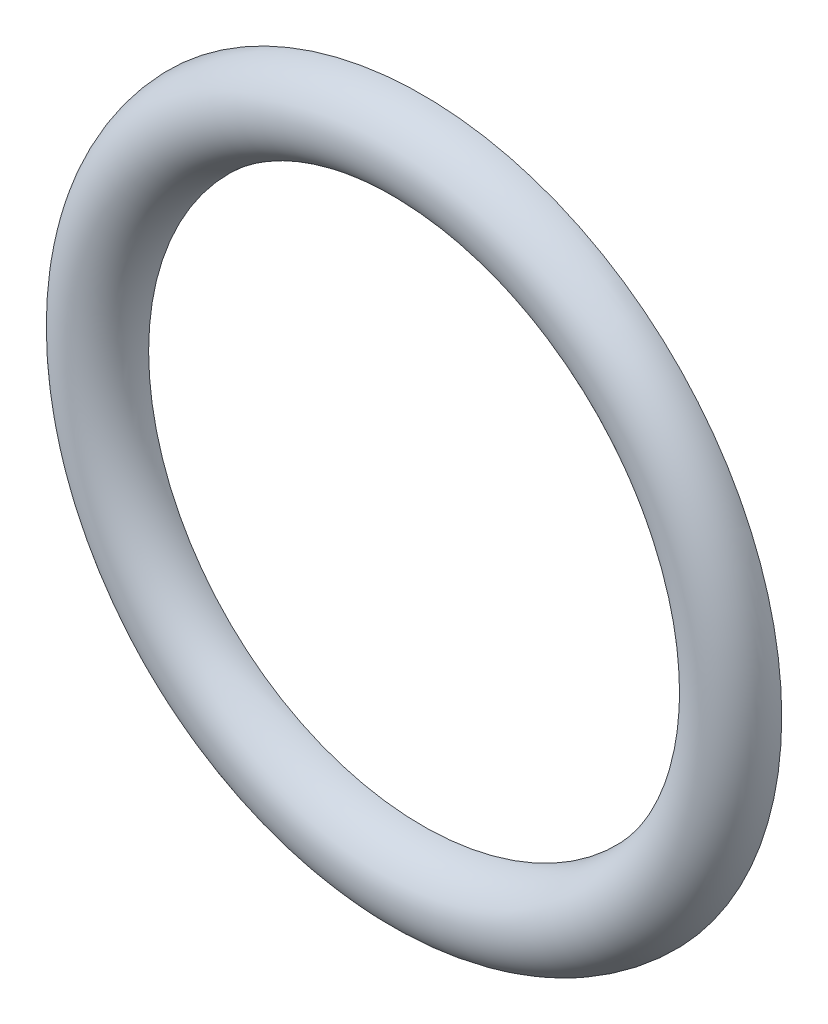
SolidWorks part; units mm, degrees
material "Delrin 2700 NC010, Low Viscosity Acetal Copolymer (SS)"
ref_plane "Front Plane" through (0, 0, 0) normal (0, 0, 1) x (1, 0, 0)
ref_plane "Top Plane" through (0, 0, 0) normal (0, 1, 0) x (1, 0, 0)
ref_plane "Right Plane" through (0, 0, 0) normal (1, 0, 0) x (0, 0, -1)
sketch "Sketch1" plane through (0, 0, 0) normal (0, 1, 0) x (1, 0, 0)
  line L0 (38.0921, 0) -> (68.0921, 0)
  line L1 (-58.9079, 53.1177) -> (-58.9079, -42.8558) construction
  arc A0 (68.0921, 0) -> (38.0921, 0) centre (53.0921, 0) cw
  dimension "D1" = 30
  dimension "D2" = 127
revolve "Revolve1" add sketch "Sketch1" angle 360 about L1
ref_plane "Plane1" through (0, 0, 15.24) normal (0, 0, -1) x (-1, 0, 0)
